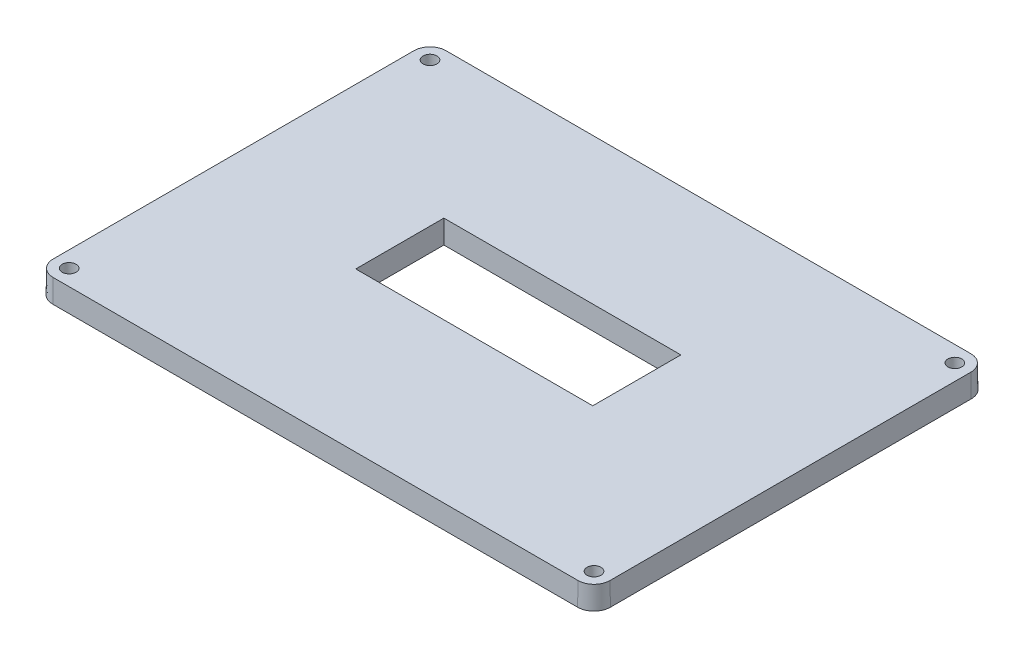
SolidWorks part; units mm, degrees
ref_plane "Front Plane" through (0, 0, 0) normal (0, 0, 1) x (1, 0, 0)
ref_plane "Top Plane" through (0, 0, 0) normal (0, 1, 0) x (1, 0, 0)
ref_plane "Right Plane" through (0, 0, 0) normal (1, 0, 0) x (0, 0, -1)
sketch "Sketch1" plane through (0, 0, 0) normal (0, 1, 0) x (1, 0, 0)
  line L1 (85, -60) -> (-85, -60)
  line L2 (85, -60) -> (85, 60)
  line L3 (85, 60) -> (-85, 60)
  line L4 (-85, -60) -> (-85, 60)
  line L5 (85, -60) -> (-85, 60) construction
  line L6 (85, 60) -> (-85, -60) construction
  point P0 (0, 0)
  dimension "D1" = 170
  dimension "D2" = 120
extrude "Boss-Extrude1" add sketch "Sketch1" along normal blind 7
sketch "Sketch2" plane through (0, 7, 0) normal (0, 1, 0) x (1, 0, 0)
  line L1 (-36, 15.2368) -> (36, 15.2368)
  line L2 (-36, 15.2368) -> (-36, -11.3838)
  line L3 (-36, -11.3838) -> (36, -11.3838)
  line L4 (36, 15.2368) -> (36, -11.3838)
  line L5 (-36, 15.2368) -> (36, -11.3838) construction
  line L6 (-36, -11.3838) -> (36, 15.2368) construction
  point P0 (0, 1.9265)
  dimension "D1" = 72
  dimension "D2" = 26.6206
extrude "Cut-Extrude1" cut sketch "Sketch2" against normal blind 7
sketch "Sketch3" plane through (0, 7, 0) normal (0, 1, 0) x (1, 0, 0)
  line L1 (85, 60) -> (-85, 60) construction
  line L2 (-85, 60) -> (-85, -60) construction
  circle A0 centre (-80, 55) radius 2
  circle A1 centre (-70, -45.36) radius 2
  dimension "D1" = 5
  dimension "D3" = 4
  dimension "D4" = 4
  dimension "D2" = 120
  dimension "D5" = 5
sketch "Sketch6" plane through (0, 7, 0) normal (0, 1, 0) x (1, 0, 0)
  line L0 (85, -60) -> (85, 60) construction
  line L1 (-85, -60) -> (85, -60) construction
  line L2 (85, 60) -> (-85, 60) construction
  circle A0 centre (80, -55) radius 2
  circle A1 centre (80, 55) radius 2
  dimension "D1" = 5
  dimension "D2" = 5
  dimension "D3" = 5
  dimension "D4" = 5
extrude "Cut-Extrude5" cut sketch "Sketch3" against normal blind 7 contours A0
sketch "Sketch7" plane through (0, 7, 0) normal (0, 1, 0) x (1, 0, 0)
  line L0 (-85, -60) -> (85, -60) construction
  line L1 (-85, 60) -> (-85, -60) construction
  circle A0 centre (-80, -55) radius 2
  dimension "D1" = 5
  dimension "D2" = 5
extrude "Cut-Extrude7" cut sketch "Sketch7" against normal blind 10
extrude "Cut-Extrude10" cut sketch "Sketch6" against normal blind 10 contours A1
sketch "Sketch9" plane through (0, 7, 0) normal (0, 1, 0) x (1, 0, 0)
  line L0 (85, -60) -> (85, 60) construction
  line L1 (-85, -60) -> (85, -60) construction
  circle A0 centre (80, -55) radius 2
  dimension "D1" = 5
  dimension "D2" = 5
extrude "Cut-Extrude11" cut sketch "Sketch9" against normal blind 10
fillet "Fillet1" radius 5 4 edges at (85, 3.5, -60) (85, 3.5, 60) (-85, 3.5, 60) (-85, 3.5, -60)
draft "Draft1" type of draft neutral plane draft angle 1 neutral plane "Top Plane" faces to draft 16 face at (-83.0178, 3.5, 58.0178) face at (-85, 3.5, 0) face at (-83.0178, 3.5, -58.0178) face at (0, 3.5, -60) face at (83.0178, 3.5, -58.0178) face at (85, 3.5, 0) face at (83.0178, 3.5, 58.0178) face at (0, 3.5, 60) face at (-80, 7, 57) face at (80, 7, 57) face at (80, 7, -53) face at (-80, 0, -53) face at (-36, 3.5, -1.9265) face at (0, 3.5, -15.2368) face at (36, 3.5, -1.9265) face at (0, 3.5, 11.3838) neutral plane through (0, 0, 0) neutral plane normal (0, 1, 0) parameters "D1"=1
